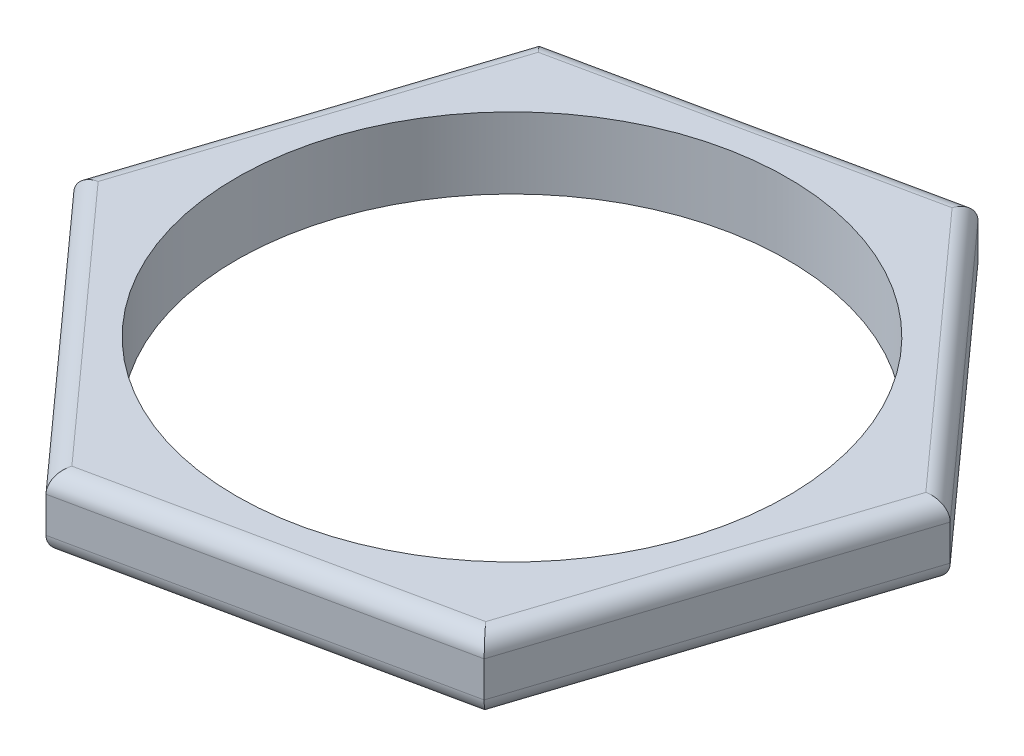
SolidWorks part; units mm, degrees
ref_plane "前视基准面" through (0, 0, 0) normal (0, 0, 1) x (1, 0, 0)
ref_plane "上视基准面" through (0, 0, 0) normal (0, 1, 0) x (1, 0, 0)
ref_plane "右视基准面" through (0, 0, 0) normal (1, 0, 0) x (0, 0, -1)
sketch "草图1" plane through (0, 0, 0) normal (0, 1, 0) x (1, 0, 0)
  line L1 (13.8946, -15.4577) -> (20.3341, 4.3042)
  line L2 (20.3341, 4.3042) -> (6.4395, 19.7619)
  line L3 (6.4395, 19.7619) -> (-13.8946, 15.4577)
  line L4 (-13.8946, 15.4577) -> (-20.3341, -4.3042)
  line L5 (-20.3341, -4.3042) -> (-6.4395, -19.7619)
  line L6 (-6.4395, -19.7619) -> (13.8946, -15.4577)
  circle A0 centre (0, 0) radius 18 construction
  circle A1 centre (0, 0) radius 15.5
  dimension "D1" = 36
  dimension "D2" = 31
extrude "凸台-拉伸1" add sketch "草图1" along normal blind 4
fillet "圆角1" radius 1 12 edges at (-17.1143, 0, -5.5768) (-13.3868, 0, 12.0331) (3.7275, 0, 17.6098) (17.1143, 0, 5.5768) (13.3868, 0, -12.0331) (-3.7275, 0, -17.6098) (-17.1143, 4, -5.5768) (-13.3868, 4, 12.0331) (3.7275, 4, 17.6098) (17.1143, 4, 5.5768) (13.3868, 4, -12.0331) (-3.7275, 4, -17.6098)
